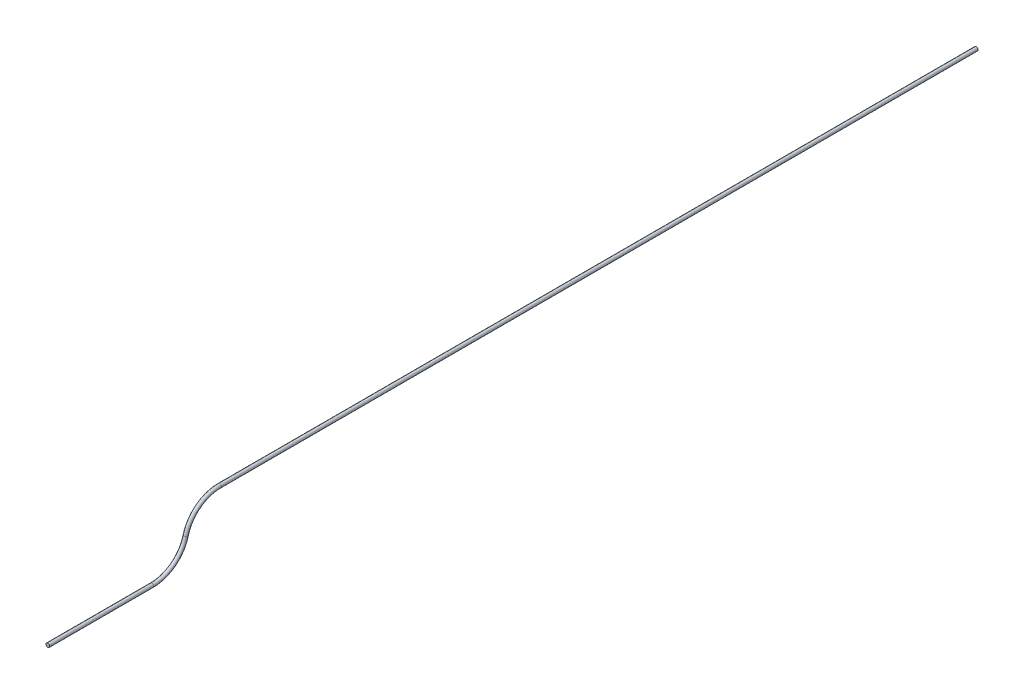
SolidWorks part; units mm, degrees
ref_plane "Front Plane" through (0, 0, 0) normal (0, 0, 1) x (1, 0, 0)
ref_plane "Top Plane" through (0, 0, 0) normal (0, 1, 0) x (1, 0, 0)
ref_plane "Right Plane" through (0, 0, 0) normal (1, 0, 0) x (0, 0, -1)
sketch "Sketch1" plane through (0, 0, 0) normal (0, 0, 1) x (1, 0, 0)
  circle A0 centre (0, 0) radius 4.0323
  dimension "D1" = 8.0645
sketch "Sketch2" plane through (0, 0, 0) normal (1, 0, 0) x (0, 0, -1)
  line L0 (0, 0) -> (227, 0)
  line L1 (374.5607, 114.3) -> (2025.5607, 114.3)
  arc A0 (227, 0) -> (300.7803, 57.15) centre (227, 76.2) ccw
  arc A1 (300.7803, 57.15) -> (374.5607, 114.3) centre (374.5607, 38.1) cw
  dimension "D3" = 76.2
  dimension "D4" = 76.2
  dimension "D1" = 227
  dimension "D2" = 114.3
  dimension "D5" = 1651
sweep "Sweep1" add profiles "Sketch1" path "Sketch2"
